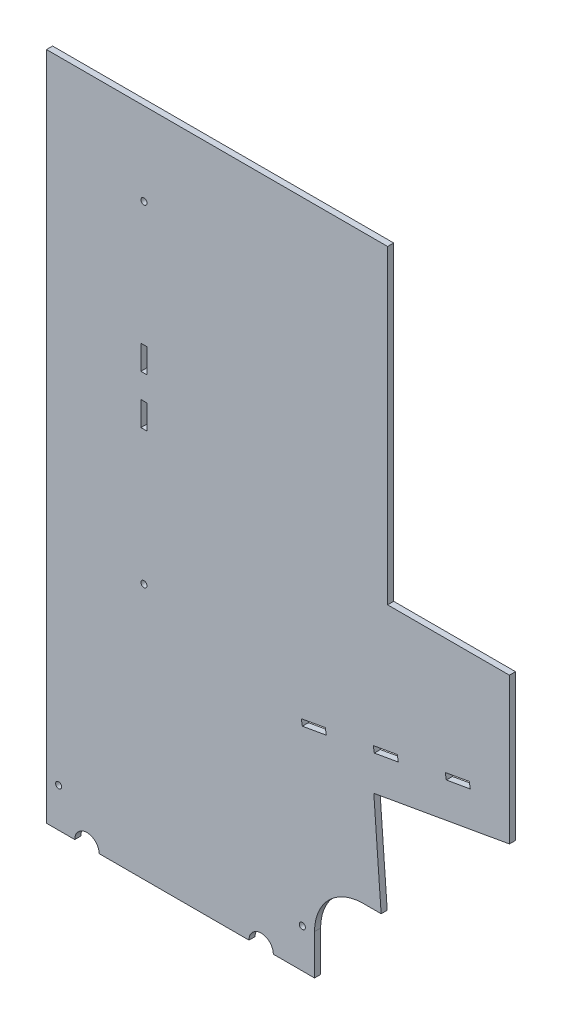
SolidWorks part; units mm, degrees
ref_plane "Front Plane" through (0, 0, 0) normal (0, 0, 1) x (1, 0, 0)
ref_plane "Top Plane" through (0, 0, 0) normal (0, 1, 0) x (1, 0, 0)
ref_plane "Right Plane" through (0, 0, 0) normal (1, 0, 0) x (0, 0, -1)
sketch "Sketch1" plane through (0, 0, 0) normal (0, 0, 1) x (1, 0, 0)
  line L0 (0, 0) -> (-177.8, 0)
  line L1 (-177.8, 0) -> (-177.8, 349.25)
  line L2 (-177.8, 349.25) -> (-25.4, 349.25)
  line L3 (-25.4, 349.25) -> (0, 0)
  dimension "D1" = 349.25
  dimension "D2" = 177.8
  dimension "D3" = 152.4
  dimension "D4" = 0
extrude "Boss-Extrude1" add sketch "Sketch1" along normal blind 3.175
sketch "Sketch2" plane through (0, 0, 3.175) normal (0, 0, 1) x (1, 0, 0)
  line L0 (-177.8, 0) -> (0, 0) construction
  circle A0 centre (-127, 133.35) radius 1.5875
  circle A1 centre (-127, 306.07) radius 1.5875
  dimension "D1" = 3.175
  dimension "D2" = 3.175
  dimension "D3" = 172.72
  dimension "D4" = 172.72
  dimension "D5" = 133.35
  dimension "D6" = 127
extrude "Cut-Extrude1" cut sketch "Sketch2" against normal blind 3.175
sketch "Sketch3" plane through (0, 0, 3.175) normal (0, 0, 1) x (1, 0, 0)
  line L1 (-63.5, 88.9) -> (63.5, 111.2935)
  line L2 (-63.5, 88.9) -> (-63.5, 187.4935)
  line L3 (-63.5, 187.4935) -> (63.5, 187.4935)
  line L4 (63.5, 111.2935) -> (63.5, 187.4935)
  line L5 (-177.8, 0) -> (0, 0) construction
  circle A0 centre (-127, 133.35) radius 1.5875 construction
  dimension "D1" = 127
  dimension "D2" = 76.2
  dimension "D3" = 44.45
  dimension "D4" = 63.5
  dimension "D5" = 10
extrude "Boss-Extrude2" add sketch "Sketch3" against normal blind 3.175
sketch "Sketch4" plane through (0, 0, 3.175) normal (0, 0, 1) x (1, 0, 0)
  line L0 (-44.45, 110.49) -> (-31.9429, 112.6953)
  line L1 (-32.4943, 115.8221) -> (-45.0013, 113.6168)
  line L2 (-45.0013, 113.6168) -> (-44.45, 110.49)
  line L3 (-32.4943, 115.8221) -> (-31.9429, 112.6953)
  line L4 (-6.9288, 117.106) -> (5.5782, 119.3113)
  line L5 (5.0269, 122.4381) -> (-7.4802, 120.2328)
  line L6 (-7.4802, 120.2328) -> (-6.9288, 117.106)
  line L7 (5.0269, 122.4381) -> (5.5782, 119.3113)
  line L8 (-7.1876, 98.8294) -> (63.5, 111.2935) construction
  circle A0 centre (-127, 133.35) radius 1.5875 construction
  dimension "D1" = 3.175
  dimension "D2" = 12.7
  dimension "D3" = 3.175
  dimension "D4" = 12.7
  dimension "D5" = 0
  dimension "D6" = 25.4
  dimension "D7" = 82.55
  dimension "D8" = 22.86
  dimension "D9" = 0
extrude "Cut-Extrude2" cut sketch "Sketch4" against normal blind 3.175
sketch "Sketch5" plane through (0, 0, 3.175) normal (0, 0, 1) x (1, 0, 0)
  line L0 (-127, 133.35) -> (-127, 306.07)
  line L1 (-128.5875, 203.2) -> (-125.4125, 203.2)
  line L2 (-125.4125, 203.2) -> (-125.4125, 215.9)
  line L3 (-125.4125, 215.9) -> (-128.5875, 215.9)
  line L4 (-128.5875, 215.9) -> (-128.5875, 203.2)
  dimension "D1" = 90
  dimension "D2" = 3.175
  dimension "D3" = 1.5875
  dimension "D4" = 69.85
  dimension "D5" = 12.7
extrude "Cut-Extrude3" cut sketch "Sketch5" against normal blind 10.16 contours L2 L3 L0 L1 | L3 L4 L1 L0
pattern_linear "LPattern1" count 2 spacing 25.4 along (0, 1, 0) of "Cut-Extrude3"
sketch "Sketch8" plane through (0, 0, 3.175) normal (0, 0, 1) x (1, 0, 0)
  line L1 (0, 0) -> (-38.1, 0)
  line L2 (0, 0) -> (0, 46.355)
  line L3 (0, 46.355) -> (-38.1, 46.355)
  line L4 (-38.1, 0) -> (-38.1, 46.355)
  dimension "D1" = 38.1
  dimension "D2" = 46.355
extrude "Cut-Extrude6" cut sketch "Sketch8" against normal blind 12.7
sketch "Sketch10" plane through (0, 0, 0) normal (0, 0, -1) x (-1, 0, 0)
  line L1 (177.8, 0) -> (38.1, 0) construction
  circle A0 centre (171.45, 20.32) radius 1.5875
  circle A1 centre (44.45, 20.32) radius 1.5875
  dimension "D1" = 3.175
  dimension "D2" = 20.32
  dimension "D3" = 6.35
  dimension "D4" = 3.175
  dimension "D5" = 20.32
  dimension "D6" = 127
extrude "Cut-Extrude7" cut sketch "Sketch10" against normal blind 7.62
sketch "Sketch11" plane through (0, 0, 0) normal (0, 0, -1) x (-1, 0, 0)
  line L1 (177.8, 0) -> (38.1, 0) construction
  circle A0 centre (156.718, 0) radius 6.35
  circle A1 centre (65.913, 0) radius 6.35
  point P8 (73.1376, 0)
  dimension "D1" = 12.7
  dimension "D2" = 0
  dimension "D3" = 90.805
  dimension "D4" = 12.7
  dimension "D5" = 21.082
  dimension "D6" = 0
extrude "Cut-Extrude8" cut sketch "Sketch11" against normal blind 12.7
fillet "Fillet1" radius 25.4 1 edges at (-38.1, 46.355, 1.5875)
sketch "Sketch13" plane through (0, 0, 0) normal (0, 0, -1) x (-1, 0, 0)
  line L0 (25.4, 349.25) -> (177.8, 349.25) construction
  line L1 (25.4, 349.25) -> (0, 349.25)
  line L2 (25.4, 349.25) -> (25.4, 171.45)
  line L3 (25.4, 171.45) -> (0, 171.45)
  line L4 (0, 349.25) -> (0, 171.45)
  dimension "D1" = 25.4
  dimension "D2" = 0
  dimension "D3" = 177.8
extrude "Boss-Extrude3" add sketch "Sketch13" against normal blind 3.175
pattern_linear "LPattern2" count 2 spacing 76.2 along (0.9848, 0.1736, 0) of "Cut-Extrude2"
